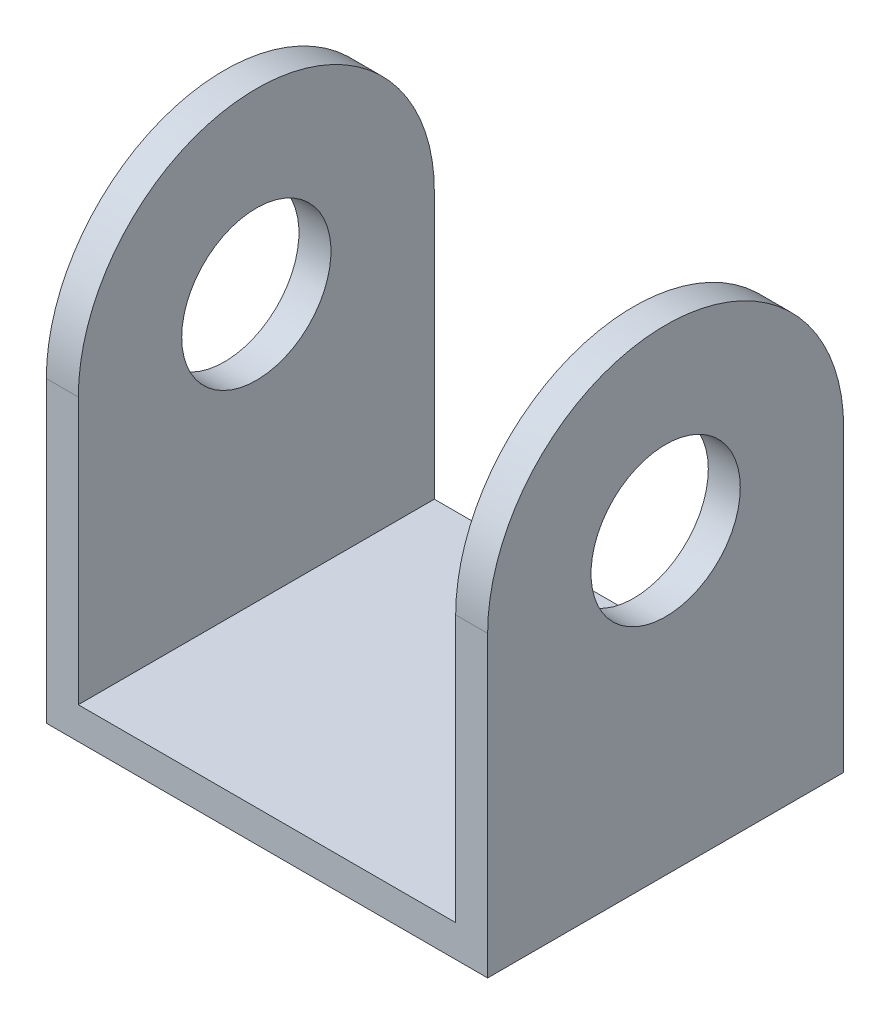
SolidWorks part; units mm, degrees
ref_plane "Alzado" through (0, 0, 0) normal (0, 0, 1) x (1, 0, 0)
ref_plane "Planta" through (0, 0, 0) normal (0, 1, 0) x (1, 0, 0)
ref_plane "Vista lateral" through (0, 0, 0) normal (1, 0, 0) x (0, 0, -1)
sketch "Croquis1" plane through (0, 0, 0) normal (1, 0, 0) x (0, 0, -1)
  line L0 (16.7, 25) -> (16.7, 0)
  line L1 (16.7, 0) -> (-16.7, 0)
  line L2 (-16.7, 25) -> (-16.7, 0)
  circle A0 centre (0, 25) radius 7
  arc A1 (16.7, 25) -> (-16.7, 25) centre (0, 25) ccw
  dimension "D3" = 16.7
  dimension "D4" = 14
  dimension "D1" = 25
  dimension "D2" = 33.4
extrude "Saliente-Extruir1" add sketch "Croquis1" along normal blind 3
sketch "Croquis2" plane through (3, 0, 0) normal (1, 0, 0) x (0, 0, -1)
  line L0 (-16.7, 0) -> (16.7, 0)
  line L1 (16.7, 0) -> (16.7, -3)
  line L2 (16.7, -3) -> (-16.7, -3)
  line L3 (-16.7, -3) -> (-16.7, 0)
  dimension "D1" = 3
extrude "Saliente-Extruir2" add sketch "Croquis2" against normal blind 41.4
sketch "Croquis3" plane through (-38.4, 0, 0) normal (-1, 0, 0) x (0, 0, 1)
  line L3 (-16.7, 25) -> (-16.7, 0)
  line L4 (16.7, -3) -> (16.7, 0)
  line L5 (16.7, 0) -> (-16.7, 0)
  line L6 (-16.7, 0) -> (-16.7, -3)
  line L7 (-16.7, -3) -> (16.7, -3)
  line L9 (16.7, 0) -> (-16.7, 0)
  line L12 (-16.7, 0) -> (16.7, 0)
  line L13 (16.7, 0) -> (16.7, 25)
  line L14 (-16.7, 25) -> (-16.7, 0)
  line L15 (-16.7, 0) -> (16.7, 0)
  line L16 (16.7, 0) -> (16.7, 25)
  circle A0 centre (0, 25) radius 7 construction
  arc A1 (16.7, 25) -> (-16.7, 25) centre (0, 25) ccw
  arc A2 (16.7, 25) -> (-16.7, 25) centre (0, 25) ccw
  circle A3 centre (0, 25) radius 7
  line M10 (16.7, 0) -> (-16.7, 0)
  dimension "D1" = 0
  dimension "D2" = 0
extrude "Saliente-Extruir3" add sketch "Croquis3" against normal blind 3 contours L16 A2 L14 A3 M10
